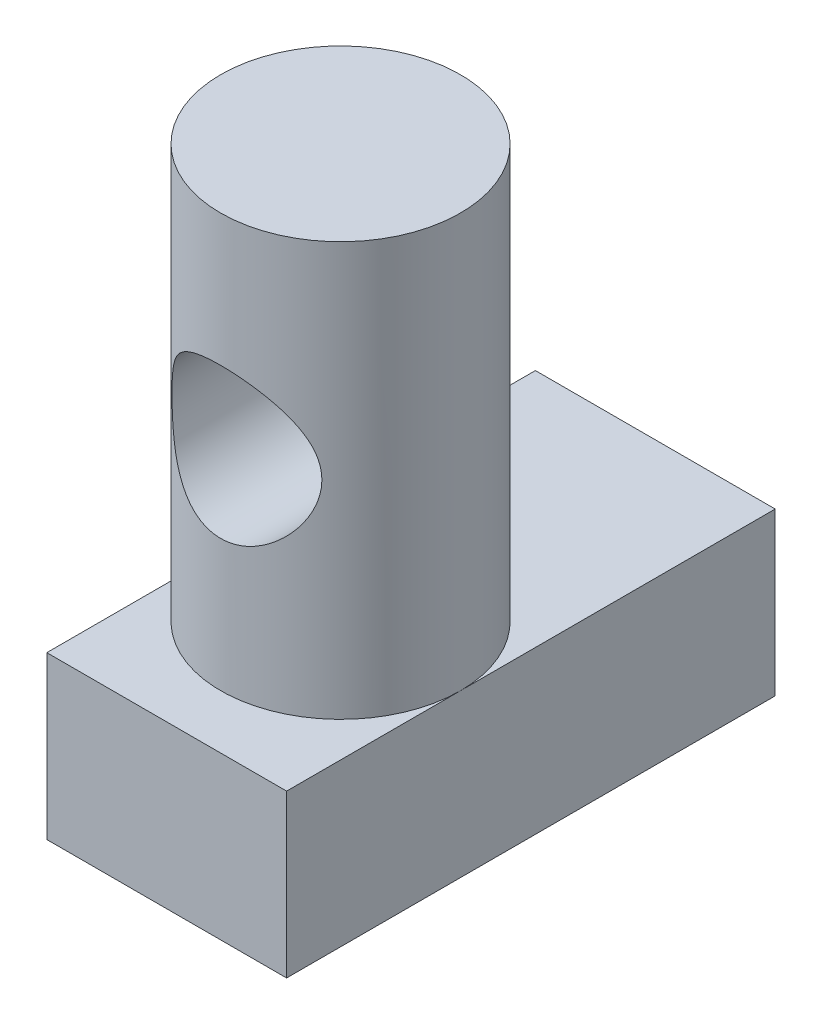
SolidWorks part; units mm, degrees
material "ABS"
ref_plane "Front Plane" through (0, 0, 0) normal (0, 0, 1) x (1, 0, 0)
ref_plane "Top Plane" through (0, 0, 0) normal (0, 1, 0) x (1, 0, 0)
ref_plane "Right Plane" through (0, 0, 0) normal (1, 0, 0) x (0, 0, -1)
sketch "Sketch2" plane through (0, 0, 0) normal (0, 1, 0) x (1, 0, 0)
  line L0 (-2, 4.075) -> (2, 4.075)
  line L1 (2, 4.075) -> (2, -4.075)
  line L2 (2, -4.075) -> (-2, -4.075)
  line L3 (-2, -4.075) -> (-2, 4.075)
  line L4 (0, 4.075) -> (0, -4.075) construction
  line L5 (2, 0) -> (-2, 0) construction
  dimension "D1" = 8.15
  dimension "D2" = 4
extrude "bottom" add sketch "Sketch2" against normal blind 2.7
sketch "Sketch3" plane through (0, 0, 0) normal (0, 1, 0) x (1, 0, 0)
  line L0 (0, 4.075) -> (0, -4.075) construction
  line L1 (2, 4.075) -> (-2, 4.075) construction
  line L2 (-2, -4.075) -> (2, -4.075) construction
  line L3 (-2, -1.175) -> (2, -1.175) construction
  line L4 (-2, 4.075) -> (-2, -4.075) construction
  line L5 (2, -4.075) -> (2, 4.075) construction
  circle A0 centre (0, -1.175) radius 2
  dimension "D1" = 4
  dimension "D2" = 2.9
extrude "top" add sketch "Sketch3" along normal blind 6.9
sketch "Sketch4" plane through (0, 0, 4.075) normal (0, 0, 1) x (1, 0, 0)
  line L0 (0, 0) -> (0, 6.9) construction
  line L2 (2, 6.9) -> (-2, 6.9) construction
  line L3 (2, 3.45) -> (-2, 3.45) construction
  line L4 (2, 0) -> (2, 6.9) construction
  line L5 (-2, 6.9) -> (-2, 0) construction
  circle A0 centre (0, 3.45) radius 1.25
  dimension "D1" = 2.5
extrude "tendon hole" cut sketch "Sketch4" against normal blind 13.5
